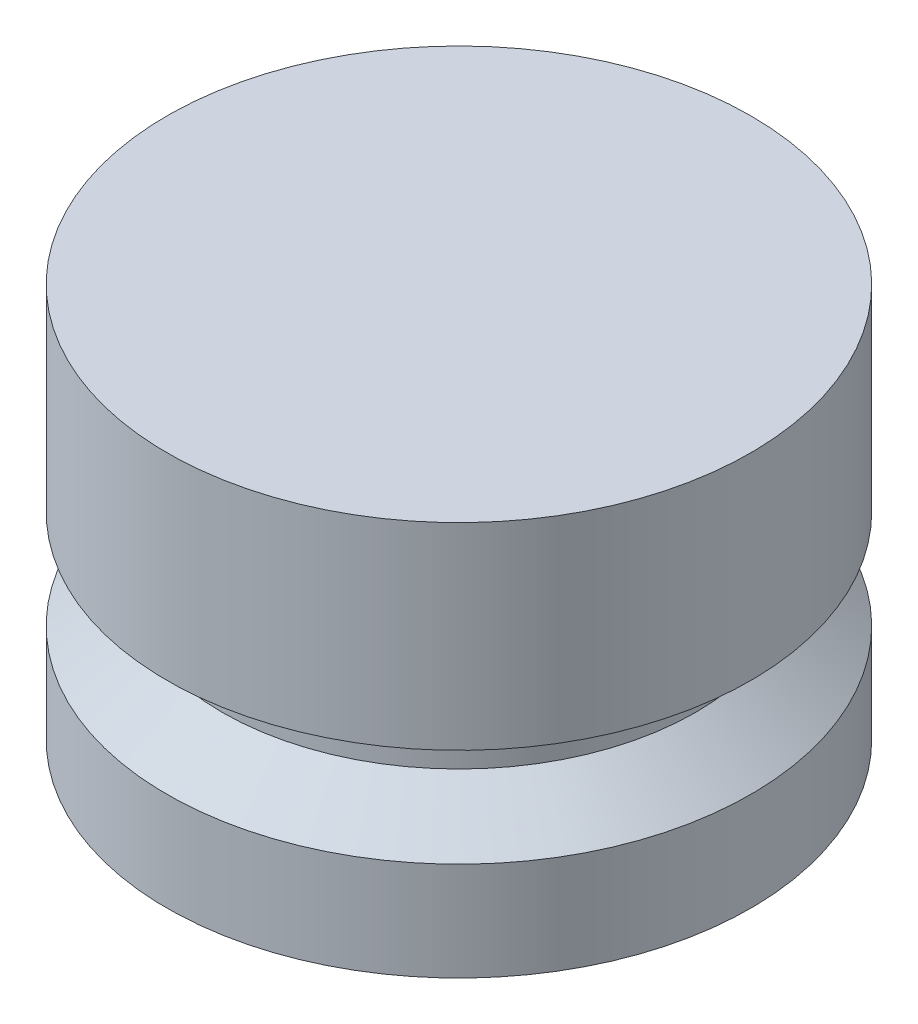
SolidWorks part; units mm, degrees
ref_plane "Front Plane" through (0, 0, 0) normal (0, 0, 1) x (1, 0, 0)
ref_plane "Top Plane" through (0, 0, 0) normal (0, 1, 0) x (1, 0, 0)
ref_plane "Right Plane" through (0, 0, 0) normal (1, 0, 0) x (0, 0, -1)
sketch "Sketch1" plane through (0, 0, 0) normal (0, 0, 1) x (1, 0, 0)
  line L0 (0, 0) -> (0, 12.7) construction
  line L1 (0, 0) -> (-9.398, 0)
  line L2 (-9.398, 0) -> (-9.398, 3.175)
  line L4 (-7.62, 4.572) -> (-7.62, 6.35)
  line L5 (-7.62, 6.35) -> (-9.398, 6.35)
  line L6 (-9.398, 6.35) -> (-9.398, 12.7)
  line L7 (-9.398, 12.7) -> (0, 12.7)
  line L8 (-9.525, 16.6801) -> (-9.525, -9.6051) construction
  line L9 (0, 0) -> (0, 12.7)
  line L10 (-7.62, 4.572) -> (-9.398, 3.175)
  dimension "D1" = 12.7
  dimension "D2" = 9.398
  dimension "D3" = 1.778
  dimension "D4" = 3.175
  dimension "D5" = 9.525
  dimension "D6" = 7.62
  dimension "D7" = 6.35
revolve "Revolve1" add sketch "Sketch1" angle 360 about L9
